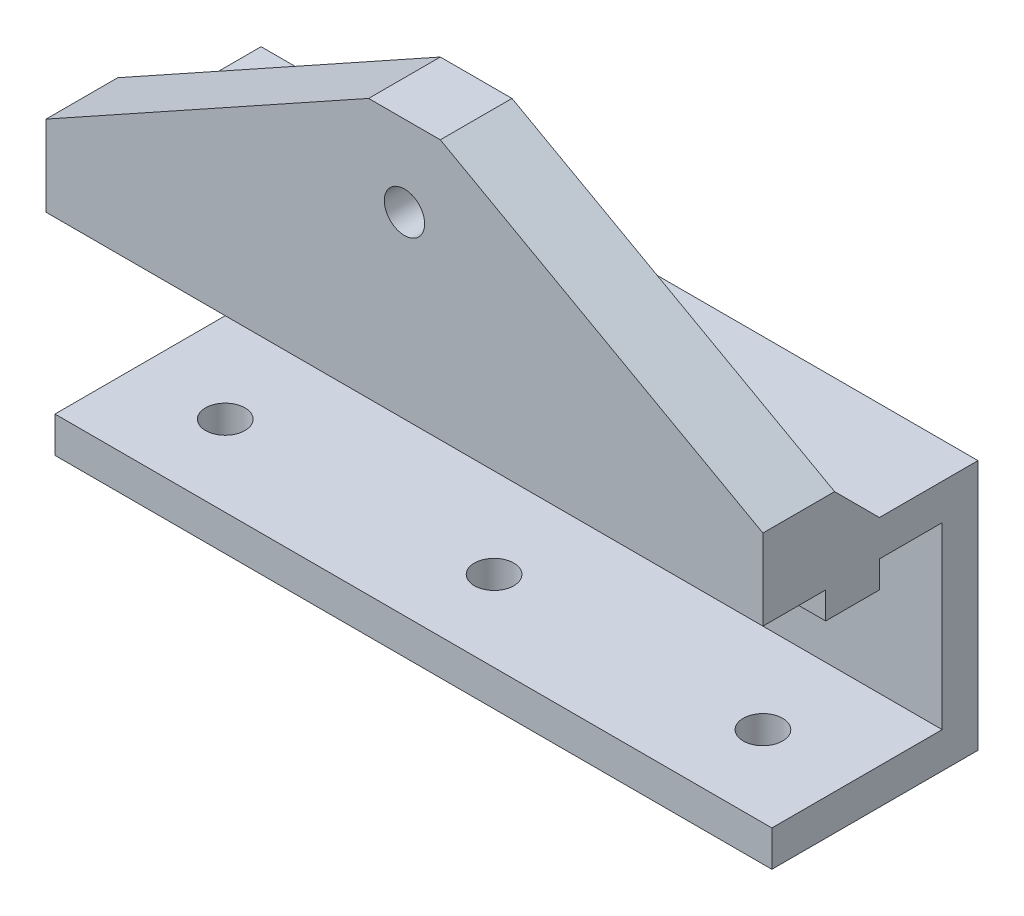
SolidWorks part; units mm, degrees
ref_plane "Plan de face" through (0, 0, 0) normal (0, 0, 1) x (1, 0, 0)
ref_plane "Plan de dessus" through (0, 0, 0) normal (0, 1, 0) x (1, 0, 0)
ref_plane "Plan de droite" through (0, 0, 0) normal (1, 0, 0) x (0, 0, -1)
sketch "Esquisse1" plane through (0, 0, 0) normal (1, 0, 0) x (0, 0, -1)
  line L0 (-33.839, -37.2656) -> (-14.839, -37.2656)
  line L1 (-14.839, -37.2656) -> (-14.839, -17.2656)
  line L2 (-14.839, -17.2656) -> (-21.839, -17.2656)
  line L3 (-21.839, -17.2656) -> (-21.839, -20.2656)
  line L4 (-21.839, -20.2656) -> (-27.839, -20.2656)
  line L5 (-27.839, -20.2656) -> (-27.839, -17.2656)
  line L6 (-27.839, -17.2656) -> (-34.839, -17.2656)
  line L7 (-34.839, -17.2656) -> (-34.839, 11.7344)
  line L8 (-34.839, 11.7344) -> (-26.839, 11.7344)
  line L9 (-26.839, 11.7344) -> (-26.839, -8.2656)
  line L10 (-21.839, -13.2656) -> (-10.839, -13.2656)
  line L11 (-10.839, -13.2656) -> (-10.839, -41.2656)
  line L12 (-10.839, -41.2656) -> (-33.839, -41.2656)
  line L13 (-33.839, -41.2656) -> (-33.839, -37.2656)
  line L14 (-26.839, -8.2656) -> (-21.839, -13.2656)
  dimension "D1" = 19
  dimension "D2" = 20
  dimension "D3" = 7
  dimension "D4" = 7
  dimension "D5" = 29
  dimension "D6" = 3
  dimension "D7" = 6
  dimension "D8" = 8
  dimension "D9" = 4
  dimension "D10" = 4
  dimension "D11" = 4
extrude "Boss.-Extru.1" add sketch "Esquisse1" along normal blind 80
sketch "Esquisse2" plane through (0, 0, 26.839) normal (0, 0, -1) x (-1, 0, 0)
  line L0 (-80, -8.2656) -> (-44, 11.7344)
  line L1 (-80, 11.7344) -> (0, 11.7344) construction
  line L2 (-44, 11.7344) -> (-36, 11.7344)
  line L3 (-36, 11.7344) -> (0, -8.2656)
  line L4 (-40, -8.2656) -> (-40, 11.7344) construction
  line L5 (-80, -8.2656) -> (0, -8.2656) construction
  line L6 (-80, -8.2656) -> (-80, 11.7344)
  line L7 (-80, 11.7344) -> (-44, 16.4369)
  line L8 (-44, 16.4369) -> (-36, 16.4369)
  line L9 (-36, 16.4369) -> (0, 11.7344)
  line L10 (0, 11.7344) -> (0, -8.2656)
  dimension "D1" = 8
extrude "Enlèv. mat.-Extru.1" cut sketch "Esquisse2" against normal through all
hole_wizard "Dégagement M41" positions "Esquisse6" profile "Esquisse5" hole size "M4" standard "Din"
sketch "Esquisse6" plane through (0, 0, 26.839) normal (0, 0, -1) x (-1, 0, 0)
  line L0 (-40, 11.7344) -> (-40, -8.2656) construction
  line L1 (-44, 11.7344) -> (-36, 11.7344) construction
  line L2 (-80, -8.2656) -> (0, -8.2656) construction
  point P0 (-40, 2.7344)
  dimension "D1" = 9
sketch "Esquisse5" plane through (40, 2.7344, 26.839) normal (1, 0, 0) x (0, 1, 0)
  line L0 (0, 0) -> (0, 11.3519)
  line L1 (0, 11.3519) -> (2.25, 10)
  line L2 (2.25, 10) -> (2.25, 0)
  line L5 (2.25, 0) -> (0, 0)
  line L10 (0, 11.3519) -> (-2.25, 10) construction
  line L11 (0, -6.35) -> (0, 107.95) construction
  dimension "Diamètre du perçage" = 4.5
  dimension "Profondeur du perçage" = 10
  dimension "Angle de pointe" = 118
sketch "Esquisse7" plane through (0, 0, 26.839) normal (0, 0, -1) x (-1, 0, 0)
  line L7 (-40, 6.7344) -> (-43.4641, 4.7344)
  line L8 (-43.4641, 4.7344) -> (-43.4641, 0.7344)
  line L9 (-43.4641, 0.7344) -> (-40, -1.2656)
  line L10 (-40, -1.2656) -> (-36.5359, 0.7344)
  line L11 (-36.5359, 0.7344) -> (-36.5359, 4.7344)
  line L12 (-36.5359, 4.7344) -> (-40, 6.7344)
  circle A1 centre (-40, 2.7344) radius 3.4641 construction
  dimension "D1" = 4
extrude "Enlèv. mat.-Extru.2" cut sketch "Esquisse7" against normal blind 4
sketch "Esquisse8" plane through (0, -41.2656, 0) normal (0, -1, 0) x (1, 0, 0)
  line L0 (80, 24.839) -> (0, 24.839) construction
  line L1 (80, 33.839) -> (80, 10.839) construction
  line L2 (0, 33.839) -> (0, 10.839) construction
  line L3 (80, 33.839) -> (0, 33.839) construction
  line L4 (40, 33.839) -> (40, 10.839) construction
  line L5 (80, 10.839) -> (0, 10.839) construction
  line L6 (10, 33.839) -> (10, 10.839) construction
  line L7 (70, 33.839) -> (70, 10.839) construction
  dimension "D1" = 9
  dimension "D2" = 30
  dimension "D3" = 30
hole_wizard "Dégagement M42" positions "Esquisse10" profile "Esquisse9" hole size "M4" standard "Din"
sketch "Esquisse10" plane through (0, -41.2656, 0) normal (0, -1, 0) x (-1, 0, 0)
  line L0 (0, -24.839) -> (-80, -24.839) construction
  line L2 (-10, -33.839) -> (-10, -10.839) construction
  line L4 (-40, -33.839) -> (-40, -10.839) construction
  line L6 (-70, -33.839) -> (-70, -10.839) construction
  line L8 (-80, -24.839) -> (0, -24.839) construction
  line L9 (-10, -33.839) -> (-10, -10.839) construction
  point P0 (-10, -24.839)
  point P2 (-40, -24.839)
  point P4 (-70, -24.839)
sketch "Esquisse9" plane through (10, -41.2656, 24.839) normal (1, 0, 0) x (0, 0, -1)
  line L0 (0, 0) -> (0, 11.3219)
  line L1 (0, 11.3219) -> (2.2, 10)
  line L2 (2.2, 10) -> (2.2, 0)
  line L5 (2.2, 0) -> (0, 0)
  line L10 (0, 11.3219) -> (-2.2, 10) construction
  line L11 (0, -6.35) -> (0, 107.95) construction
  dimension "Diamètre du perçage" = 4.4
  dimension "Profondeur du perçage" = 10
  dimension "Angle de pointe" = 118
move or copy body "Corps-Déplacer/Copier1" [suppressed] bodies to move or copy 106
